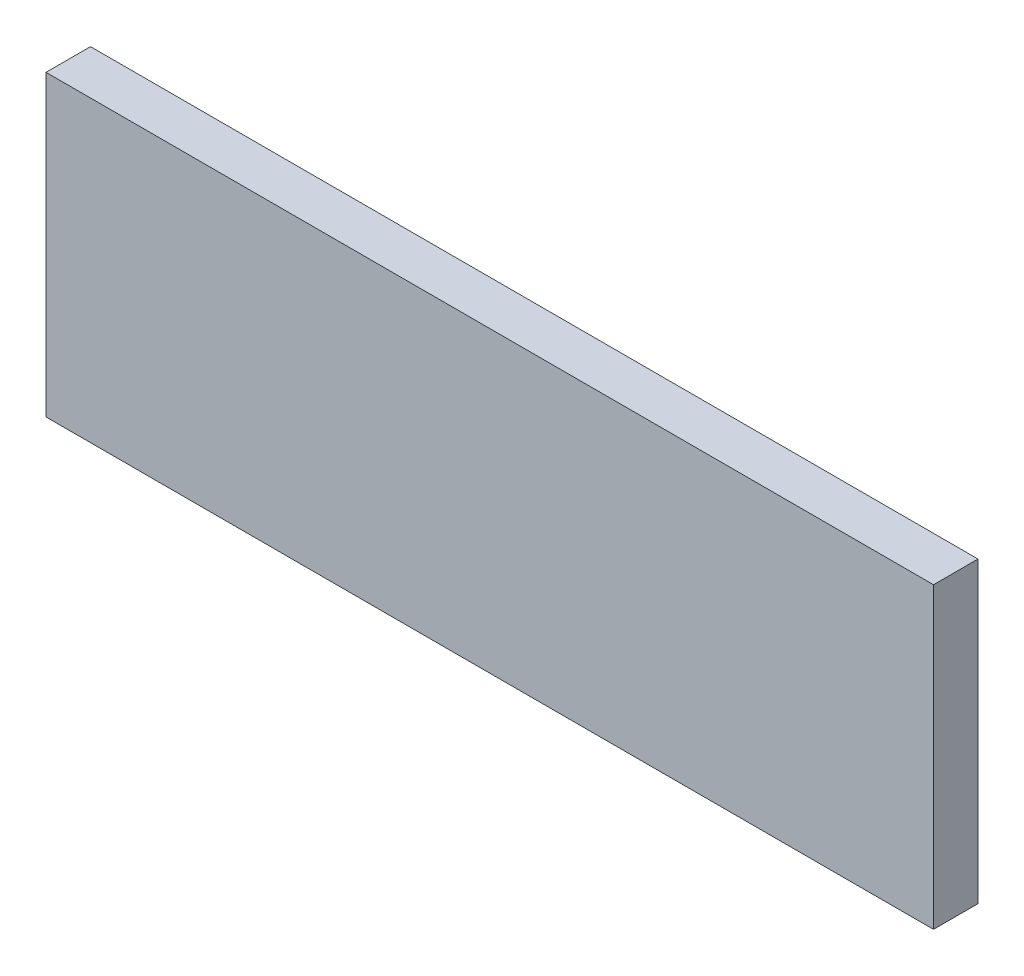
SolidWorks part; units mm, degrees
ref_plane "Front Plane" through (0, 0, 0) normal (0, 0, 1) x (1, 0, 0)
ref_plane "Top Plane" through (0, 0, 0) normal (0, 1, 0) x (1, 0, 0)
ref_plane "Right Plane" through (0, 0, 0) normal (1, 0, 0) x (0, 0, -1)
sketch "Sketch1" plane through (0, 0, 0) normal (0, 0, 1) x (1, 0, 0)
  line L1 (-95, 31.95) -> (95, 31.95)
  line L2 (-95, 31.95) -> (-95, -31.95)
  line L3 (-95, -31.95) -> (95, -31.95)
  line L4 (95, 31.95) -> (95, -31.95)
  point P4 (-95, 0)
  point P8 (0, -31.95)
  dimension "D1" = 190
  dimension "D2" = 63.9
extrude "Boss-Extrude1" add sketch "Sketch1" along normal blind 9.525
sketch "Sketch2" plane through (0, -31.95, 0) normal (0, -1, 0) x (1, 0, 0)
  line L0 (95, 9.525) -> (95, 0) construction
  point P0 (71.25, 4.7625)
  point P1 (0, 4.7625)
  point P2 (-71.25, 4.7625)
  point P6 (95, 4.7625)
  dimension "D1" = 71.25
  dimension "D2" = 71.25
  dimension "D3" = 23.75
hole_wizard "Tap Drill for M4 Tap1" positions "Sketch3" profile "Sketch4" hole size "M4" standard "ISO"
sketch "Sketch3" plane through (0, -31.95, 0) normal (0, -1, 0) x (-1, 0, 0)
  point P0 (-71.25, -4.7625)
  point P3 (0, -4.7625)
  point P6 (71.25, -4.7625)
sketch "Sketch4" plane through (71.25, -31.95, 4.7625) normal (1, 0, 0) x (0, 0, -1)
  line L0 (0, 0) -> (0, 13.6914)
  line L1 (0, 13.6914) -> (1.65, 12.7)
  line L2 (1.65, 12.7) -> (1.65, 0)
  line L5 (1.65, 0) -> (0, 0)
  line L10 (0, 13.6914) -> (-1.65, 12.7) construction
  line L11 (0, -6.35) -> (0, 107.95) construction
  dimension "Hole Dia." = 3.3
  dimension "Hole Depth" = 12.7
  dimension "Drill Angle" = 118
